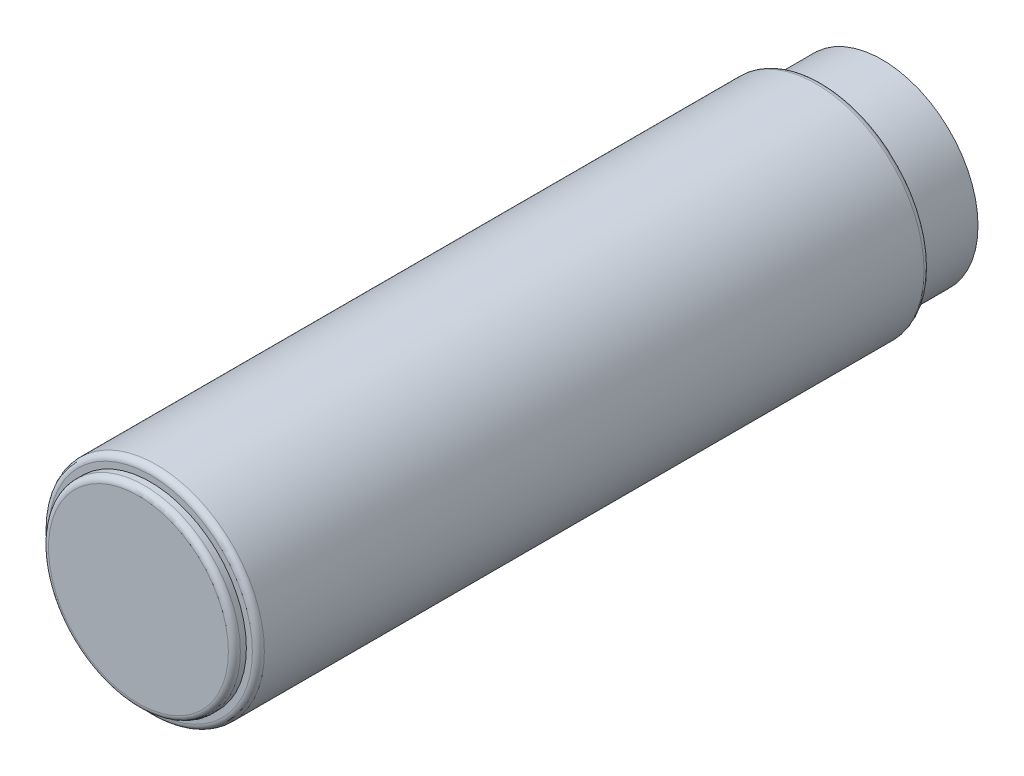
SolidWorks part; units mm, degrees
ref_plane "Plan de face" through (0, 0, 0) normal (0, 0, 1) x (1, 0, 0)
ref_plane "Plan de dessus" through (0, 0, 0) normal (0, 1, 0) x (1, 0, 0)
ref_plane "Plan de droite" through (0, 0, 0) normal (1, 0, 0) x (0, 0, -1)
sketch "Esquisse1" plane through (0, 0, 0) normal (0, 0, 1) x (1, 0, 0)
  circle A0 centre (0, 0) radius 9
  dimension "D1" = 18
extrude "Boss.-Extru.1" add sketch "Esquisse1" along normal blind 56
sketch "Esquisse2" plane through (0, 0, 56) normal (0, 0, 1) x (1, 0, 0)
  circle A0 centre (0, 0) radius 8
  dimension "D1" = 16
extrude "Boss.-Extru.2" add sketch "Esquisse2" along normal blind 1 separate body
sketch "Esquisse3" plane through (0, 0, 0) normal (0, 0, -1) x (-1, 0, 0)
  circle A0 centre (0, 0) radius 8
  dimension "D1" = 16
extrude "Boss.-Extru.3" add sketch "Esquisse3" along normal blind 5 separate body
fillet "Congé1" radius 0.5 1 edges at (8, 0, 57)
fillet "Congé2" radius 0.5 1 edges at (9, 0, 56)
fillet "Congé3" radius 0.5 1 edges at (9, 0, 0)
